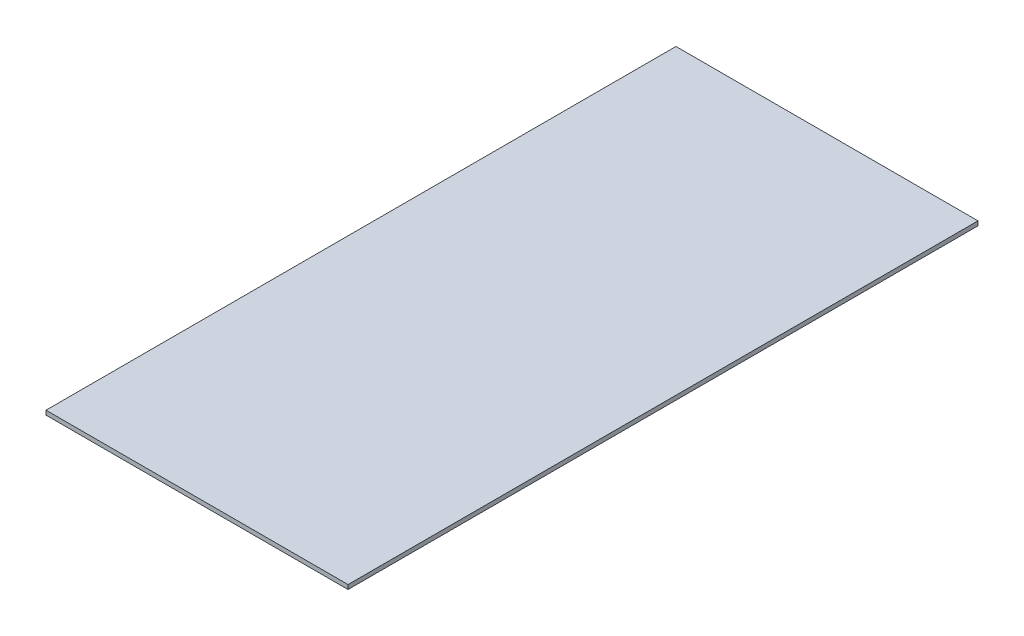
SolidWorks part; units mm, degrees
material "PVC Rigid"
ref_plane "Front Plane" through (0, 0, 0) normal (0, 0, 1) x (1, 0, 0)
ref_plane "Top Plane" through (0, 0, 0) normal (0, 1, 0) x (1, 0, 0)
ref_plane "Right Plane" through (0, 0, 0) normal (1, 0, 0) x (0, 0, -1)
sketch "Sketch1" plane through (0, 0, 0) normal (0, 1, 0) x (1, 0, 0)
  line L1 (-191.9561, 88.6169) -> (-14.1561, 88.6169)
  line L2 (-191.9561, 88.6169) -> (-191.9561, -282.2231)
  line L3 (-191.9561, -282.2231) -> (-14.1561, -282.2231)
  line L4 (-14.1561, 88.6169) -> (-14.1561, -282.2231)
  dimension "D1" = 177.8
  dimension "D2" = 370.84
extrude "Boss-Extrude1" add sketch "Sketch1" along normal blind 2.54
